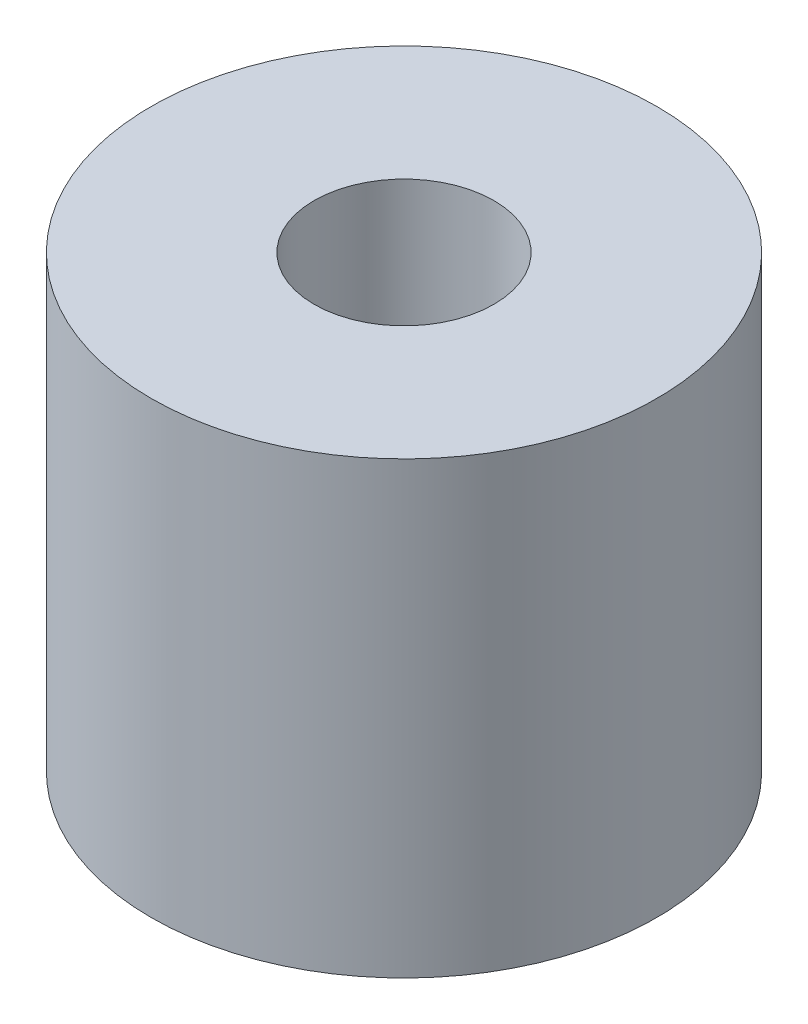
SolidWorks part; units mm, degrees
ref_plane "Alzado" through (0, 0, 0) normal (0, 0, 1) x (1, 0, 0)
ref_plane "Planta" through (0, 0, 0) normal (0, 1, 0) x (1, 0, 0)
ref_plane "Vista lateral" through (0, 0, 0) normal (1, 0, 0) x (0, 0, -1)
sketch "Croquis1" plane through (0, 0, 0) normal (0, 1, 0) x (1, 0, 0)
  circle A0 centre (0, 0) radius 4.5
  circle A1 centre (0, 0) radius 1.6
  dimension "D1" = 9
  dimension "D2" = 3.2
extrude "Saliente-Extruir1" add sketch "Croquis1" along normal blind 8
